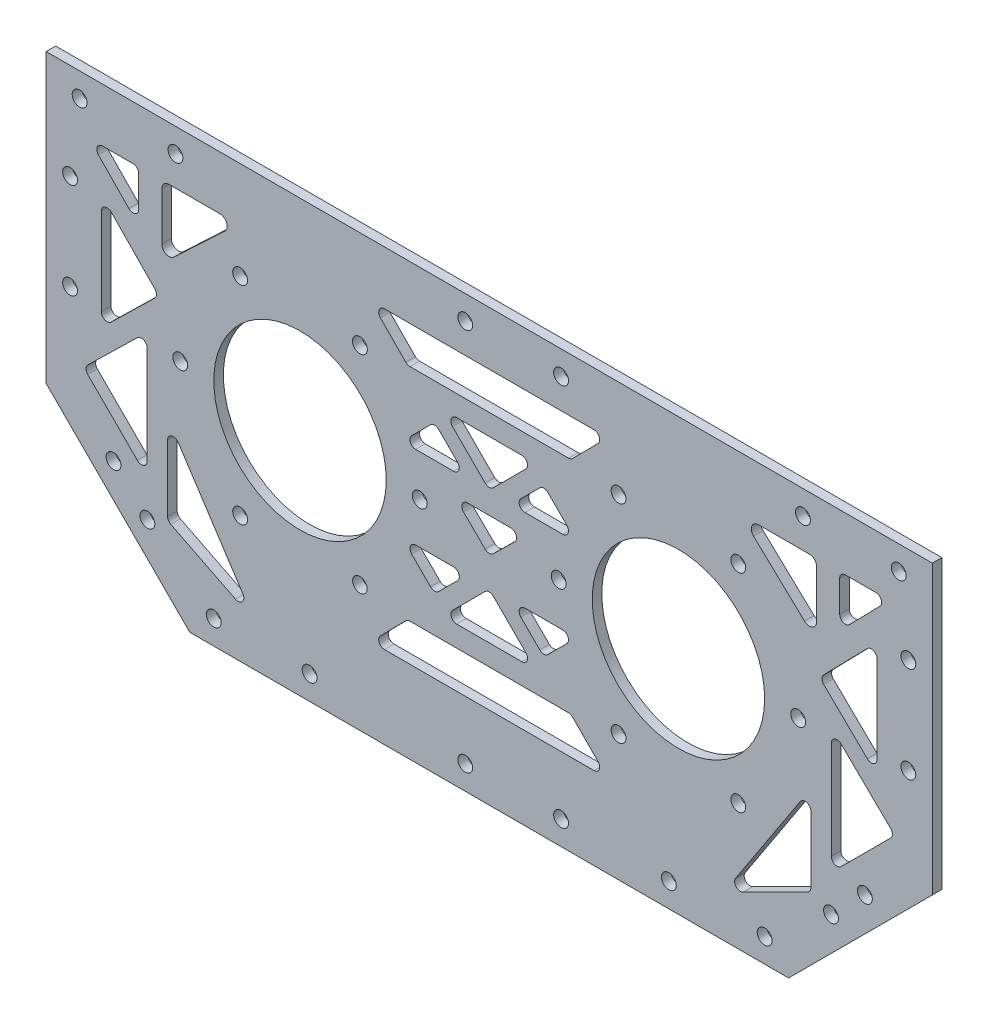
SolidWorks part; units mm, degrees
material "Thornel Mat VMA"
ref_plane "前视基准面" through (0, 0, 0) normal (0, 0, 1) x (1, 0, 0)
ref_plane "上视基准面" through (0, 0, 0) normal (0, 1, 0) x (1, 0, 0)
ref_plane "右视基准面" through (0, 0, 0) normal (1, 0, 0) x (0, 0, -1)
sketch "草图1" plane through (0, 0, 0) normal (0, 0, 1) x (1, 0, 0)
  line L0 (-39.5, 0) -> (39.5, 0) construction
  line L4 (-92.5, 18) -> (-92.5, -18)
  line L5 (-62.5, -48) -> (62.5, -48)
  line L6 (92.5, 18) -> (92.5, -18)
  line L8 (-62.5, 32.4324) -> (70.1149, -36.3839) construction
  line L9 (-39.5, 0) -> (-52, -21.6506) construction
  line L10 (-39.5, 0) -> (-39.5, -25) construction
  line L11 (-52, 21.6506) -> (-27, -21.6506) construction
  line L12 (-39.5, 0) -> (-27, 21.6506) construction
  line L13 (39.5, 0) -> (27, -21.6506) construction
  line L14 (39.5, 0) -> (52, -21.6506) construction
  line L15 (39.5, 0) -> (39.5, -25) construction
  line L16 (39.5, 0) -> (52, 21.6506) construction
  line L17 (27, 21.6506) -> (39.5, 0) construction
  line L18 (39.5, 0) -> (64.5, 0) construction
  line L19 (-92.5, 42) -> (-92.5, 18)
  line L21 (-62.5, -32.4324) -> (62.5, 32.4324) construction
  line L22 (92.5, 42) -> (92.5, 18)
  line L23 (62.5, -48) -> (62.5, 48) construction
  line L24 (-62.5, -48) -> (-62.5, 48) construction
  line L25 (0, 48) -> (0, -63.7675) construction
  line L26 (92.5, -18) -> (62.5, -48)
  line L27 (-20, -40) -> (20, -40) construction
  line L28 (-20, -40) -> (-20, -46) construction
  line L29 (-20, -46) -> (20, -46) construction
  line L30 (20, -40) -> (20, -46) construction
  line L31 (-20, -40) -> (20, -46) construction
  line L32 (-20, -46) -> (20, -40) construction
  line L33 (-92.5, -18) -> (-62.5, -48)
  line L34 (-92.5, 42) -> (92.5, 42)
  line L36 (92.5, -18) -> (62.5, -18) construction
  line L38 (-62.5, -18) -> (-92.5, -18) construction
  circle A16 centre (-39.5, 0) radius 25 construction
  circle A17 centre (39.5, 0) radius 25 construction
  circle A22 centre (-64.5, 0) radius 1.55
  circle A23 centre (-14.5, 0) radius 1.55
  circle A24 centre (14.5, 0) radius 1.55
  circle A25 centre (64.5, 0) radius 1.55
  circle A26 centre (27, 21.6506) radius 1.55
  circle A27 centre (52, 21.6506) radius 1.55
  circle A28 centre (52, -21.6506) radius 1.55
  circle A29 centre (27, -21.6506) radius 1.55
  circle A30 centre (-52, -21.6506) radius 1.55
  circle A33 centre (-52, 21.6506) radius 1.55
  circle A34 centre (-27, -21.6506) radius 1.51
  circle A35 centre (-27, 21.6506) radius 1.55
  circle A48 centre (-39.5, 0) radius 18
  circle A49 centre (39.5, 0) radius 18
  circle A50 centre (57.5, -43) radius 1.55
  circle A51 centre (37.5, -43) radius 1.55
  circle A52 centre (-57.5, -43) radius 1.55
  circle A53 centre (-37.5, -43) radius 1.55
  circle A54 centre (-85.5, 37) radius 1.55
  circle A55 centre (-65.5, 37) radius 1.55
  circle A56 centre (65.5, 37) radius 1.55
  circle A57 centre (85.5, 37) radius 1.55
  circle A58 centre (15, -43) radius 1.55
  circle A59 centre (-5, -43) radius 1.55
  circle A60 centre (-5, 37) radius 1.55
  circle A61 centre (15, 37) radius 1.55
  circle A70 centre (78.4289, -25) radius 1.55
  circle A71 centre (71.3579, -32.0711) radius 1.55
  circle A72 centre (-78.4289, -25) radius 1.55
  circle A73 centre (-71.3579, -32.0711) radius 1.55
  point P0 (0, 0)
  point P9 (0, 0)
  point P51 (-39.5, 0)
  point P77 (0, -43)
  point P122 (-14.5, -16.9833)
  point P132 (0, -16.9833)
  point P137 (0, -23.1315)
  point P149 (0, -25.9696)
  point P152 (0, -34.7247)
  point P155 (0, 18)
  point P158 (0, 21.8042)
  point P161 (0, 29.7291)
  point P163 (0, 10.0782)
  point P171 (-10.5486, 5.4739)
  dimension "D4" = 3.1
  dimension "D5" = 30
  dimension "D6" = 30
  dimension "D8" = 30
  dimension "D12" = 5
  dimension "D20" = 7
  dimension "D16" = 5
  dimension "D30" = 5
  dimension "D32" = 3.1
  dimension "D34" = 3.1
  dimension "D36" = 5
  dimension "D40" = 5
  dimension "D44" = 5
  dimension "D33" = 3.1
  dimension "D1" = 79
  dimension "D7" = 60
  dimension "D9" = 30
  dimension "D10" = 60
  dimension "D11" = 60
  dimension "D13" = 5
  dimension "D14" = 20
  dimension "D15" = 5
  dimension "D17" = 20
  dimension "D18" = 5
  dimension "D19" = 5
  dimension "D21" = 20
  dimension "D22" = 5
  dimension "D23" = 5
  dimension "D24" = 5
  dimension "D25" = 5
  dimension "D26" = 7
  dimension "D27" = 20
  dimension "D28" = 40
  dimension "D29" = 6
  dimension "D31" = 20
  dimension "D35" = 5
  dimension "D37" = 10
  dimension "D38" = 7
  dimension "D39" = 5
  dimension "D41" = 7
  dimension "D42" = 10
  dimension "D43" = 90
  dimension "D45" = 20
  dimension "D46" = 5
extrude "凸台-拉伸1" add sketch "草图1" along normal blind 2
sketch "草图2" plane through (0, 0, 2) normal (0, 0, 1) x (1, 0, 0)
  line L0 (92.5, 42) -> (-92.5, 42) construction
  line L5 (92.5, -18) -> (92.5, 42) construction
  line L6 (-92.5, 42) -> (-92.5, -18) construction
  line L7 (0, 58.1343) -> (0, -64.0698) construction
  line L10 (21.8679, 30.8057) -> (-21.8679, 30.8057)
  line L11 (-22.723, 28.7638) -> (-17.4139, 23.3715)
  line L12 (-16.5588, 23.0134) -> (16.5588, 23.0134)
  line L13 (6.8106, 18.6571) -> (-6.8106, 18.6571)
  line L14 (-7.6592, 16.6086) -> (-0.8485, 9.798)
  line L15 (-10.5519, 14.6475) -> (-6.6006, 10.6962)
  line L16 (-7.4491, 8.6476) -> (-15.3518, 8.6476)
  line L17 (-16.2003, 10.6962) -> (-12.2489, 14.6475)
  line L18 (7.4491, 8.6476) -> (15.3518, 8.6476)
  line L19 (10.5519, 14.6475) -> (6.6006, 10.6962)
  line L20 (16.2003, 10.6962) -> (12.2489, 14.6475)
  line L21 (7.6592, 16.6086) -> (0.8485, 9.798)
  line L22 (22.723, 28.7638) -> (17.4139, 23.3715)
  line L23 (4.5234, 4.3787) -> (-4.5234, 4.3787)
  line L24 (-5.366, 2.3243) -> (-0.8426, -2.1367)
  line L25 (5.366, 2.3243) -> (0.8426, -2.1367)
  line L26 (0, 0) -> (157.6823, 0) construction
  line L27 (-7.4491, -8.6476) -> (-15.3518, -8.6476)
  line L28 (-10.5519, -14.6475) -> (-6.6006, -10.6962)
  line L29 (-16.2003, -10.6962) -> (-12.2489, -14.6475)
  line L30 (10.5519, -14.6475) -> (6.6006, -10.6962)
  line L31 (16.2003, -10.6962) -> (12.2489, -14.6475)
  line L32 (7.4491, -8.6476) -> (15.3518, -8.6476)
  line L33 (6.8106, -18.6571) -> (-6.8106, -18.6571)
  line L34 (-7.6592, -16.6086) -> (-0.8485, -9.798)
  line L35 (7.6592, -16.6086) -> (0.8485, -9.798)
  line L36 (22.723, -28.7638) -> (17.4139, -23.3715)
  line L37 (21.8679, -30.8057) -> (-21.8679, -30.8057)
  line L38 (-22.723, -28.7638) -> (-17.4139, -23.3715)
  line L39 (-16.5588, -23.0134) -> (16.5588, -23.0134)
  line L55 (74.3669, 30.8057) -> (80.7213, 30.8057)
  line L56 (81.58, 28.7675) -> (75.2256, 22.2575)
  line L57 (73.1669, 23.0957) -> (73.1669, 29.6057)
  line L58 (78.9155, 19.7701) -> (69.8129, 10.4447)
  line L59 (73.4497, -0.2048) -> (83.8082, -10.3157)
  line L60 (80.9742, 18.9319) -> (80.9742, 0.7215)
  line L61 (83.8186, -12.023) -> (73.46, -22.3816)
  line L62 (71.4115, -21.533) -> (71.4115, -1.0635)
  line L63 (69.8335, 8.7477) -> (78.936, -0.1372)
  line L64 (62.5, -48) -> (92.5, -18) construction
  line L65 (67.1422, -15.5288) -> (67.1422, -29.3964)
  line L66 (66.48, -30.4691) -> (52.9689, -37.2425)
  line L67 (51.4271, -35.5125) -> (64.9382, -14.8716)
  line L68 (-66.48, -30.4691) -> (-52.9689, -37.2425)
  line L69 (-67.1422, -15.5288) -> (-67.1422, -29.3964)
  line L70 (-51.4271, -35.5125) -> (-64.9382, -14.8716)
  line L71 (-83.8186, -12.023) -> (-73.46, -22.3816)
  line L72 (-73.4497, -0.2048) -> (-83.8082, -10.3157)
  line L73 (-71.4115, -21.533) -> (-71.4115, -1.0635)
  line L74 (-78.9155, 19.7701) -> (-69.8129, 10.4447)
  line L75 (-80.9742, 18.9319) -> (-80.9742, 0.7215)
  line L76 (-69.8335, 8.7477) -> (-78.936, -0.1372)
  line L77 (-81.58, 28.7675) -> (-75.2256, 22.2575)
  line L78 (-74.3669, 30.8057) -> (-80.7213, 30.8057)
  line L79 (-73.1669, 23.0957) -> (-73.1669, 29.6057)
  line L83 (-68.3509, 29.3057) -> (-68.3509, 19.2695)
  line L84 (-65.8218, 18.1782) -> (-55.179, 28.2144)
  line L85 (-56.2081, 30.8057) -> (-66.8509, 30.8057)
  line L86 (65.8218, 18.1782) -> (55.179, 28.2144)
  line L87 (68.3509, 29.3057) -> (68.3509, 19.2695)
  line L88 (56.2081, 30.8057) -> (66.8509, 30.8057)
  circle A0 centre (87.5, 22) radius 1.55
  circle A1 centre (87.5, 2) radius 1.55
  circle A2 centre (-87.5, 22) radius 1.55
  circle A3 centre (-87.5, 2) radius 1.55
  arc A5 (-22.723, 28.7638) -> (-21.8679, 30.8057) centre (-21.8679, 29.6057) cw
  arc A6 (-17.4139, 23.3715) -> (-16.5588, 23.0134) centre (-16.5588, 24.2134) ccw
  arc A7 (-7.6592, 16.6086) -> (-6.8106, 18.6571) centre (-6.8106, 17.4571) cw
  arc A8 (-7.4491, 8.6476) -> (-6.6006, 10.6962) centre (-7.4491, 9.8476) ccw
  arc A9 (-16.2003, 10.6962) -> (-15.3518, 8.6476) centre (-15.3518, 9.8476) ccw
  arc A10 (-10.5519, 14.6475) -> (-12.2489, 14.6475) centre (-11.4004, 13.799) ccw
  arc A11 (7.4491, 8.6476) -> (6.6006, 10.6962) centre (7.4491, 9.8476) cw
  arc A12 (16.2003, 10.6962) -> (15.3518, 8.6476) centre (15.3518, 9.8476) cw
  arc A13 (10.5519, 14.6475) -> (12.2489, 14.6475) centre (11.4004, 13.799) cw
  arc A14 (7.6592, 16.6086) -> (6.8106, 18.6571) centre (6.8106, 17.4571) ccw
  arc A15 (17.4139, 23.3715) -> (16.5588, 23.0134) centre (16.5588, 24.2134) cw
  arc A16 (22.723, 28.7638) -> (21.8679, 30.8057) centre (21.8679, 29.6057) ccw
  arc A17 (0.8485, 9.798) -> (-0.8485, 9.798) centre (0, 10.6465) cw
  arc A18 (-5.366, 2.3243) -> (-4.5234, 4.3787) centre (-4.5234, 3.1787) cw
  arc A19 (5.366, 2.3243) -> (4.5234, 4.3787) centre (4.5234, 3.1787) ccw
  arc A20 (0.8426, -2.1367) -> (-0.8426, -2.1367) centre (0, -1.2824) cw
  arc A21 (-7.4491, -8.6476) -> (-6.6006, -10.6962) centre (-7.4491, -9.8476) cw
  arc A22 (-16.2003, -10.6962) -> (-15.3518, -8.6476) centre (-15.3518, -9.8476) cw
  arc A23 (-10.5519, -14.6475) -> (-12.2489, -14.6475) centre (-11.4004, -13.799) cw
  arc A24 (7.4491, -8.6476) -> (6.6006, -10.6962) centre (7.4491, -9.8476) ccw
  arc A25 (10.5519, -14.6475) -> (12.2489, -14.6475) centre (11.4004, -13.799) ccw
  arc A26 (16.2003, -10.6962) -> (15.3518, -8.6476) centre (15.3518, -9.8476) ccw
  arc A27 (7.6592, -16.6086) -> (6.8106, -18.6571) centre (6.8106, -17.4571) cw
  arc A28 (-7.6592, -16.6086) -> (-6.8106, -18.6571) centre (-6.8106, -17.4571) ccw
  arc A29 (0.8485, -9.798) -> (-0.8485, -9.798) centre (0, -10.6465) ccw
  arc A30 (22.723, -28.7638) -> (21.8679, -30.8057) centre (21.8679, -29.6057) cw
  arc A31 (-22.723, -28.7638) -> (-21.8679, -30.8057) centre (-21.8679, -29.6057) ccw
  arc A32 (-17.4139, -23.3715) -> (-16.5588, -23.0134) centre (-16.5588, -24.2134) cw
  arc A33 (17.4139, -23.3715) -> (16.5588, -23.0134) centre (16.5588, -24.2134) ccw
  arc A46 (83.8082, -10.3157) -> (83.8186, -12.023) centre (82.97, -11.1745) cw
  arc A47 (71.4115, -21.533) -> (73.46, -22.3816) centre (72.6115, -21.533) ccw
  arc A48 (71.4115, -1.0635) -> (73.4497, -0.2048) centre (72.6115, -1.0635) cw
  arc A49 (80.9742, 0.7215) -> (78.936, -0.1372) centre (79.7742, 0.7215) cw
  arc A50 (69.8335, 8.7477) -> (69.8129, 10.4447) centre (70.6717, 9.6065) cw
  arc A51 (78.9155, 19.7701) -> (80.9742, 18.9319) centre (79.7742, 18.9319) cw
  arc A52 (80.7213, 30.8057) -> (81.58, 28.7675) centre (80.7213, 29.6057) cw
  arc A53 (75.2256, 22.2575) -> (73.1669, 23.0957) centre (74.3669, 23.0957) cw
  arc A54 (73.1669, 29.6057) -> (74.3669, 30.8057) centre (74.3669, 29.6057) cw
  arc A58 (67.1422, -29.3964) -> (66.48, -30.4691) centre (65.9422, -29.3964) cw
  arc A59 (51.4271, -35.5125) -> (52.9689, -37.2425) centre (52.4311, -36.1698) ccw
  arc A60 (67.1422, -15.5288) -> (64.9382, -14.8716) centre (65.9422, -15.5288) ccw
  arc A61 (-67.1422, -29.3964) -> (-66.48, -30.4691) centre (-65.9422, -29.3964) ccw
  arc A62 (-51.4271, -35.5125) -> (-52.9689, -37.2425) centre (-52.4311, -36.1698) cw
  arc A63 (-67.1422, -15.5288) -> (-64.9382, -14.8716) centre (-65.9422, -15.5288) cw
  arc A64 (-83.8082, -10.3157) -> (-83.8186, -12.023) centre (-82.97, -11.1745) ccw
  arc A65 (-71.4115, -21.533) -> (-73.46, -22.3816) centre (-72.6115, -21.533) cw
  arc A66 (-71.4115, -1.0635) -> (-73.4497, -0.2048) centre (-72.6115, -1.0635) ccw
  arc A67 (-78.9155, 19.7701) -> (-80.9742, 18.9319) centre (-79.7742, 18.9319) ccw
  arc A68 (-80.9742, 0.7215) -> (-78.936, -0.1372) centre (-79.7742, 0.7215) ccw
  arc A69 (-69.8335, 8.7477) -> (-69.8129, 10.4447) centre (-70.6717, 9.6065) ccw
  arc A70 (-80.7213, 30.8057) -> (-81.58, 28.7675) centre (-80.7213, 29.6057) ccw
  arc A71 (-75.2256, 22.2575) -> (-73.1669, 23.0957) centre (-74.3669, 23.0957) ccw
  arc A72 (-73.1669, 29.6057) -> (-74.3669, 30.8057) centre (-74.3669, 29.6057) ccw
  arc A76 (-56.2081, 30.8057) -> (-55.179, 28.2144) centre (-56.2081, 29.3057) cw
  arc A77 (-68.3509, 19.2695) -> (-65.8218, 18.1782) centre (-66.8509, 19.2695) ccw
  arc A78 (-68.3509, 29.3057) -> (-66.8509, 30.8057) centre (-66.8509, 29.3057) cw
  arc A79 (68.3509, 19.2695) -> (65.8218, 18.1782) centre (66.8509, 19.2695) cw
  arc A80 (56.2081, 30.8057) -> (55.179, 28.2144) centre (56.2081, 29.3057) ccw
  arc A81 (68.3509, 29.3057) -> (66.8509, 30.8057) centre (66.8509, 29.3057) ccw
  point P53 (0, 18.6571)
  point P54 (0, 23.0134)
  point P59 (0, 30.8057)
  point P61 (0, 8.9494)
  point P68 (0, 4.3787)
  point P70 (0, -2.9678)
  point P140 (73.1669, 20.1483)
  point P147 (68.8372, 20.1483)
  point P150 (68.8372, 30.8057)
  dimension "D7" = 1.2
  dimension "D8" = 1.2
  dimension "D9" = 1.2
  dimension "D10" = 1.2
  dimension "D11" = 1.2
  dimension "D12" = 1.2
  dimension "D13" = 1.5
  dimension "D1" = 20
  dimension "D2" = 20
  dimension "D3" = 20
  dimension "D4" = 20
  dimension "D5" = 5
  dimension "D6" = 5
extrude "切除-拉伸1" cut sketch "草图2" against normal blind 10
